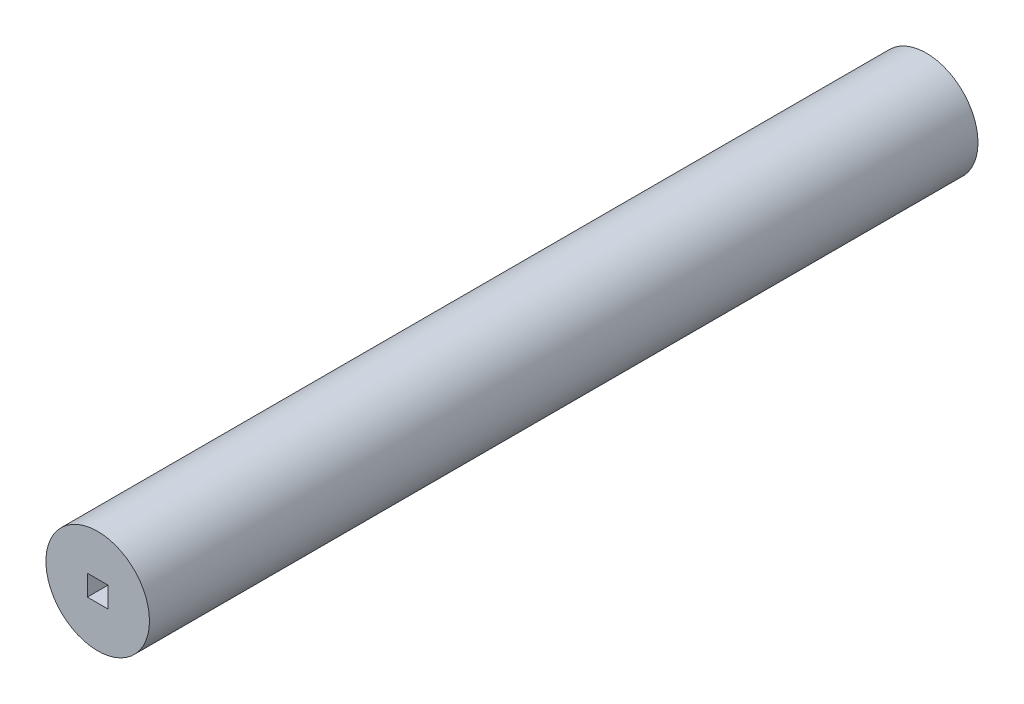
SolidWorks part; units mm, degrees
ref_plane "Front Plane" through (0, 0, 0) normal (0, 0, 1) x (1, 0, 0)
ref_plane "Top Plane" through (0, 0, 0) normal (0, 1, 0) x (1, 0, 0)
ref_plane "Right Plane" through (0, 0, 0) normal (1, 0, 0) x (0, 0, -1)
sketch "Sketch1" plane through (0, 0, 0) normal (0, 0, 1) x (1, 0, 0)
  circle A0 centre (0, 0) radius 7.9375
  dimension "D1" = 15.875
extrude "Boss-Extrude1" add sketch "Sketch1" along normal blind 127
sketch "Sketch2" plane through (0, 0, 127) normal (0, 0, 1) x (1, 0, 0)
  line L1 (0, 1.5875) -> (1.5875, 1.5875)
  line L2 (1.5875, 1.5875) -> (1.5875, -1.5875)
  line L3 (1.5875, -1.5875) -> (-1.5875, -1.5875)
  line L4 (-1.5875, -1.5875) -> (-1.5875, 1.5875)
  line L5 (-1.5875, 1.5875) -> (0, 1.5875)
  dimension "D2" = 1.5875
  dimension "D3" = 1.5875
  dimension "D4" = 3.175
  dimension "D5" = 3.175
  dimension "D6" = 3.175
extrude "Cut-Extrude1" cut sketch "Sketch2" against normal through all
